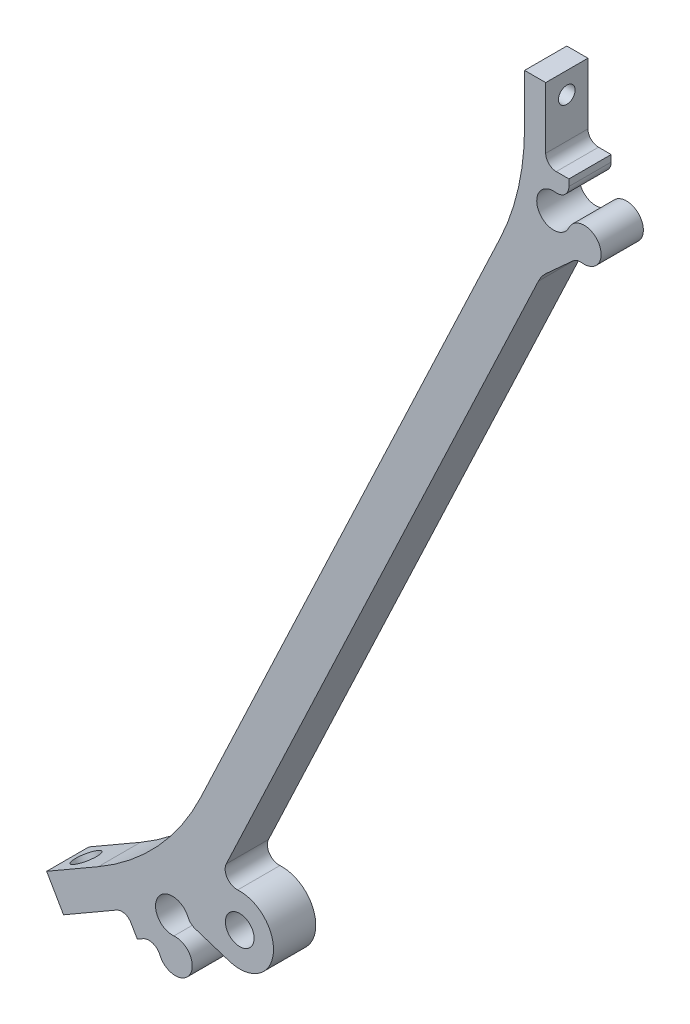
SolidWorks part; units mm, degrees
material "6061-T6 (SS)"
ref_plane "Front Plane" through (0, 0, 0) normal (0, 0, 1) x (1, 0, 0)
ref_plane "Top Plane" through (0, 0, 0) normal (0, 1, 0) x (1, 0, 0)
ref_plane "Right Plane" through (0, 0, 0) normal (1, 0, 0) x (0, 0, -1)
sketch "Sketch1" plane through (0, 0, 0) normal (0, 0, 1) x (1, 0, 0)
  line L0 (0, 0) -> (183.642, 142.5448) construction
  line L1 (0, 0) -> (183.642, 0) construction
  line L2 (0, 0) -> (0, 142.5448) construction
  line L3 (0, 142.5448) -> (183.642, 142.5448) construction
  line L4 (183.642, 0) -> (183.642, 142.5448) construction
  line L5 (91.821, 187.5086) -> (91.821, 71.2724) construction
  line L6 (91.821, 71.2724) -> (192.4845, 13.1543) construction
  line L7 (91.821, 71.2724) -> (-8.8425, 13.1543) construction
  line L8 (17.6741, 34.5985) -> (23.7376, 24.0962) construction
  line L9 (15.8347, 31.4345) -> (25.1835, 36.832)
  line L10 (25.1835, 36.832) -> (26.9297, 33.8074)
  line L11 (26.9297, 33.8074) -> (37.9282, 40.1574) construction
  line L12 (40.3017, 50.3021) -> (87.2277, 149.6422)
  line L13 (91.821, 152.5524) -> (91.821, 165.2524) construction
  line L14 (91.821, 165.2524) -> (88.3285, 165.2524)
  line L15 (97.0619, 172.8724) -> (88.3285, 172.8724) construction
  line L16 (88.3285, 165.2524) -> (88.3285, 176.0474)
  line L17 (88.3285, 176.0474) -> (85.1535, 176.0474)
  line L18 (85.1535, 176.0474) -> (85.1535, 160.1182)
  line L19 (85.1535, 160.1182) -> (31.3755, 46.2729)
  line L20 (31.3755, 46.2729) -> (13.2947, 35.8339)
  line L21 (13.2947, 35.8339) -> (15.8347, 31.4345)
  line L22 (91.821, 165.2524) -> (91.821, 164.2635)
  line L23 (91.821, 153.5413) -> (91.821, 152.5524) construction
  line L24 (26.9297, 33.8074) -> (27.7861, 34.3018)
  line L25 (37.9282, 40.1574) -> (37.0719, 39.663) construction
  line L26 (32.2093, 39.5129) -> (32.6487, 34.4519) construction
  line L27 (89.5197, 159.9774) -> (94.1223, 157.8274) construction
  line L28 (35.6392, 39.5099) -> (40.7743, 37.8607)
  line L29 (92.4048, 154.8585) -> (88.409, 151.236)
  circle A0 centre (91.821, 71.2724) radius 116.2362 construction
  arc A1 (37.7343, 44.8672) -> (37.9282, 40.1574) centre (42.3276, 42.6974) ccw construction
  arc A2 (91.821, 152.5524) -> (87.2277, 149.6422) centre (91.821, 147.4724) ccw construction
  arc A3 (89.8275, 162.4987) -> (91.821, 158.9024) centre (89.5197, 159.9774) ccw
  arc A4 (93.8145, 155.3061) -> (91.821, 158.9024) centre (94.1223, 157.8274) ccw
  arc A5 (93.8145, 155.3061) -> (91.821, 153.5413) centre (93.599, 153.5413) ccw construction
  arc A6 (91.821, 164.2635) -> (89.8275, 162.4987) centre (90.043, 164.2635) cw
  arc A7 (30.3113, 33.4579) -> (32.429, 36.9824) centre (32.6487, 34.4519) ccw
  arc A8 (34.5467, 40.5069) -> (32.429, 36.9824) centre (32.2093, 39.5129) ccw
  arc A9 (37.0719, 39.663) -> (34.5467, 40.5069) centre (36.1829, 41.2028) cw construction
  arc A10 (27.7861, 34.3018) -> (30.3113, 33.4579) centre (28.6751, 32.762) cw
  arc A11 (40.7743, 37.8607) -> (42.0178, 47.7679) centre (42.3276, 42.6974) ccw
  circle A12 centre (42.3276, 42.6974) radius 2.159
  arc A13 (40.3017, 50.3021) -> (42.0178, 47.7679) centre (41.9093, 49.5426) ccw
  arc A14 (34.5467, 40.5069) -> (35.6392, 39.5099) centre (36.1829, 41.2028) ccw
  arc A15 (87.2277, 149.6422) -> (88.409, 151.236) centre (91.821, 147.4724) cw
  arc A16 (93.8145, 155.3061) -> (92.4048, 154.8585) centre (93.599, 153.5413) ccw
  point P37 (91.821, 155.0924)
  point P40 (91.821, 162.7124)
  point P48 (19.2308, 29.3624)
  point P51 (29.1294, 35.0774)
  point P53 (32.429, 36.9824)
  point P54 (91.821, 158.9024)
  dimension "D18" = 5.08
  dimension "D20" = 1.778
  dimension "D22" = 1.778
  dimension "D23" = 5.08
  dimension "D24" = 3.302
  dimension "D25" = 3.302
  dimension "D26" = 4.318
  dimension "D27" = 1.778
  dimension "D1" = 183.642
  dimension "D2" = 142.5448
  dimension "D3" = 120
  dimension "D4" = 120
  dimension "D5" = 82.55
  dimension "D6" = 3.175
  dimension "D7" = 6.35
  dimension "D8" = 12.7
  dimension "D9" = 7.62
  dimension "D10" = 3.175
  dimension "D11" = 5.08
  dimension "D12" = 6.985
  dimension "D13" = 6.985
  dimension "D14" = 12.7
  dimension "D15" = 101.6
  dimension "D16" = 7.62
  dimension "D17" = 3.175
  dimension "D19" = 2.54
  dimension "D21" = 2.54
extrude "Boss-Extrude1" add sketch "Sketch1" along normal blind 6.35
sketch "Sketch2" plane through (-9.6529, 16.7192, 0) normal (0.5, -0.866, 0) x (-0.866, -0.5, 0)
  line L0 (-29.4305, -6.35) -> (-29.4305, 0) construction
  circle A0 centre (-32.6055, -3.175) radius 1.8288
  point P2 (-29.4305, -3.175)
  dimension "D1" = 3.6576
  dimension "D2" = 3.175
extrude "Cut-Extrude1" cut sketch "Sketch2" against normal through all
sketch "Sketch3" plane through (88.3285, 0, 0) normal (1, 0, 0) x (0, 0, -1)
  line L0 (-6.35, 176.0474) -> (0, 176.0474) construction
  circle A0 centre (-3.175, 172.8724) radius 0.635
  point P2 (-3.175, 176.0474)
  dimension "D1" = 1.27
  dimension "D2" = 3.175
extrude "Cut-Extrude2" cut sketch "Sketch3" against normal through all
fillet "Fillet1" radius 1.5875 2 edges at (25.1835, 36.832, 3.175) (88.3285, 165.2524, 3.175)
fillet "Fillet2" radius 38.1 2 edges at (85.1535, 160.1182, 3.175) (31.3755, 46.2729, 3.175)
hole_wizard "M3x0.5 Tapped Hole1" positions "Sketch5" profile "Sketch4" tap size "M3x0.5" standard "ANSI Metric"
sketch "Sketch5" plane through (85.1535, 0, 0) normal (-1, 0, 0) x (0, 0, 1)
  point P0 (3.175, 172.8724)
sketch "Sketch4" plane through (85.1535, 172.8724, 3.175) normal (0, 1, 0) x (0, 0, 1)
  line L0 (0, 0) -> (0, 8.2517)
  line L1 (0, 8.2517) -> (1.25, 7.5006)
  line L2 (1.25, 7.5006) -> (1.25, 0)
  line L5 (1.25, 0) -> (0, 0)
  line L10 (0, 8.2517) -> (-1.25, 7.5006) construction
  line L11 (0, -6.35) -> (0, 107.95) construction
  dimension "Tap Drill Dia." = 2.5
  dimension "Tap Drill Depth" = 7.5006
  dimension "Drill Angle" = 118
cosmetic thread "Hole Thread2" parameters "D1"=5.08, "D2"=3
